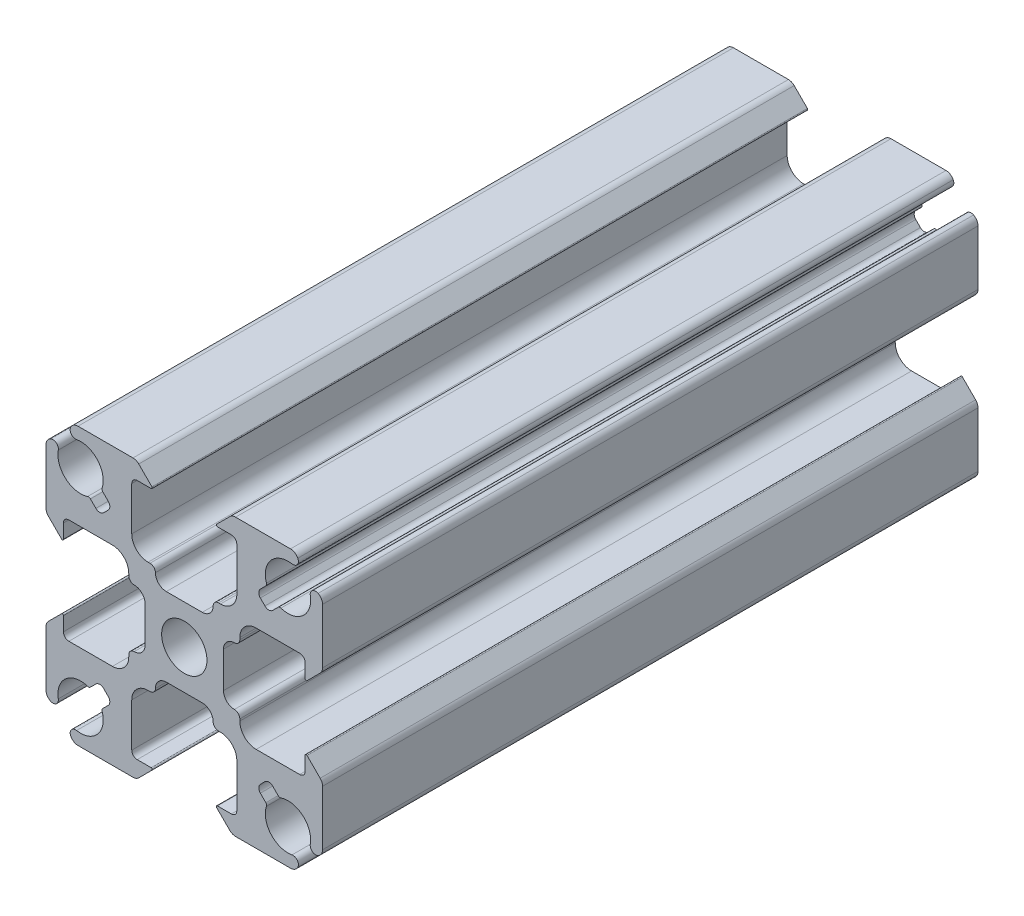
SolidWorks part; units mm, degrees
ref_plane "Front Plane" through (0, 0, 0) normal (0, 0, 1) x (1, 0, 0)
ref_plane "Top Plane" through (0, 0, 0) normal (0, 1, 0) x (1, 0, 0)
ref_plane "Right Plane" through (0, 0, 0) normal (1, 0, 0) x (0, 0, -1)
ref_plane "Plane1" through (0, 0, 0) normal (0, 0, -1) x (-1, 0, 0)
sketch "Sketch1" plane through (0, 0, 0) normal (0, 0, -1) x (-1, 0, 0)
  line L0 (-7.4885, 8.6199) -> (-6.9856, 8.117)
  line L1 (-6.9856, 7.4099) -> (-7.4099, 6.9856)
  line L2 (-8.117, 6.9856) -> (-8.6199, 7.4885)
  line L3 (-12.7, 9.7594) -> (-12.7, 4.7107)
  line L4 (-12.4803, 4.1803) -> (-11.2707, 2.9707)
  line L5 (-11.1, 3.0414) -> (-11.1, 4.325)
  line L6 (-10.6, 4.825) -> (-6.6, 4.825)
  line L7 (-5.1, 3.325) -> (-5.1, 3.15)
  line L8 (-3.6, 1.65) -> (-3.6, -1.65)
  line L9 (-5.1, -3.15) -> (-5.1, -3.325)
  line L10 (-6.6, -4.825) -> (-10.6, -4.825)
  line L11 (-11.1, -4.325) -> (-11.1, -3.0414)
  line L12 (-11.2707, -2.9707) -> (-12.4803, -4.1803)
  line L13 (-12.7, -4.7107) -> (-12.7, -9.7594)
  line L14 (-8.6199, -7.4885) -> (-8.117, -6.9856)
  line L15 (-7.4099, -6.9856) -> (-6.9856, -7.4099)
  line L16 (-6.9856, -8.117) -> (-7.4885, -8.6199)
  line L17 (-9.7594, -12.7) -> (-4.7107, -12.7)
  line L18 (-4.1803, -12.4803) -> (-2.9707, -11.2707)
  line L19 (-3.0414, -11.1) -> (-4.325, -11.1)
  line L20 (-4.825, -10.6) -> (-4.825, -6.6)
  line L21 (-3.325, -5.1) -> (-3.15, -5.1)
  line L22 (-1.65, -3.6) -> (1.65, -3.6)
  line L23 (3.15, -5.1) -> (3.325, -5.1)
  line L24 (4.825, -6.6) -> (4.825, -10.6)
  line L25 (4.325, -11.1) -> (3.0414, -11.1)
  line L26 (2.9707, -11.2707) -> (4.1803, -12.4803)
  line L27 (4.7107, -12.7) -> (9.7594, -12.7)
  line L28 (7.4885, -8.6199) -> (6.9856, -8.117)
  line L29 (6.9856, -7.4099) -> (7.4099, -6.9856)
  line L30 (8.117, -6.9856) -> (8.6199, -7.4885)
  line L31 (12.7, -9.7594) -> (12.7, -4.7107)
  line L32 (12.4803, -4.1803) -> (11.2707, -2.9707)
  line L33 (11.1, -3.0414) -> (11.1, -4.325)
  line L34 (10.6, -4.825) -> (6.6, -4.825)
  line L35 (5.1, -3.325) -> (5.1, -3.15)
  line L36 (3.6, -1.65) -> (3.6, 1.65)
  line L37 (5.1, 3.15) -> (5.1, 3.325)
  line L38 (6.6, 4.825) -> (10.6, 4.825)
  line L39 (11.1, 4.325) -> (11.1, 3.0414)
  line L40 (11.2707, 2.9707) -> (12.4803, 4.1803)
  line L41 (12.7, 4.7107) -> (12.7, 9.7594)
  line L42 (8.6199, 7.4885) -> (8.117, 6.9856)
  line L43 (7.4099, 6.9856) -> (6.9856, 7.4099)
  line L44 (6.9856, 8.117) -> (7.4885, 8.6199)
  line L45 (9.7594, 12.7) -> (4.7107, 12.7)
  line L46 (4.1803, 12.4803) -> (2.9707, 11.2707)
  line L47 (3.0414, 11.1) -> (4.325, 11.1)
  line L48 (4.825, 10.6) -> (4.825, 6.6)
  line L49 (3.325, 5.1) -> (3.15, 5.1)
  line L50 (1.65, 3.6) -> (-1.65, 3.6)
  line L51 (-3.15, 5.1) -> (-3.325, 5.1)
  line L52 (-4.825, 6.6) -> (-4.825, 10.6)
  line L53 (-4.325, 11.1) -> (-3.0414, 11.1)
  line L54 (-2.9707, 11.2707) -> (-4.1803, 12.4803)
  line L55 (-4.7107, 12.7) -> (-9.7594, 12.7)
  circle A0 centre (0, 0) radius 2.08
  arc A1 (-9.7594, 12.7) -> (-10.4266, 12.2927) centre (-9.7594, 11.95) ccw
  arc A2 (-10.4266, 12.2927) -> (-9.8933, 11.5721) centre (-9.9818, 12.0642) ccw
  arc A3 (-9.8933, 11.5721) -> (-7.5492, 8.8748) centre (-9.525, 9.525) cw
  arc A4 (-7.5492, 8.8748) -> (-7.4885, 8.6199) centre (-7.3118, 8.7967) ccw
  arc A5 (-6.9856, 8.117) -> (-6.9856, 7.4099) centre (-7.3392, 7.7635) cw
  arc A6 (-7.4099, 6.9856) -> (-8.117, 6.9856) centre (-7.7635, 7.3392) cw
  arc A7 (-8.6199, 7.4885) -> (-8.8748, 7.5492) centre (-8.7967, 7.3118) ccw
  arc A8 (-8.8748, 7.5492) -> (-11.5721, 9.8933) centre (-9.525, 9.525) cw
  arc A9 (-11.5721, 9.8933) -> (-12.2927, 10.4266) centre (-12.0642, 9.9818) ccw
  arc A10 (-12.2927, 10.4266) -> (-12.7, 9.7594) centre (-11.95, 9.7594) ccw
  arc A11 (-12.7, 4.7107) -> (-12.4803, 4.1803) centre (-11.95, 4.7107) ccw
  arc A12 (-11.2707, 2.9707) -> (-11.1, 3.0414) centre (-11.2, 3.0414) ccw
  arc A13 (-11.1, 4.325) -> (-10.6, 4.825) centre (-10.6, 4.325) cw
  arc A14 (-6.6, 4.825) -> (-5.1, 3.325) centre (-6.6, 3.325) cw
  arc A15 (-5.1, 3.15) -> (-4.6, 2.65) centre (-4.6, 3.15) ccw
  arc A16 (-4.6, 2.65) -> (-3.6, 1.65) centre (-4.6, 1.65) cw
  arc A17 (-3.6, -1.65) -> (-4.6, -2.65) centre (-4.6, -1.65) cw
  arc A18 (-4.6, -2.65) -> (-5.1, -3.15) centre (-4.6, -3.15) ccw
  arc A19 (-5.1, -3.325) -> (-6.6, -4.825) centre (-6.6, -3.325) cw
  arc A20 (-10.6, -4.825) -> (-11.1, -4.325) centre (-10.6, -4.325) cw
  arc A21 (-11.1, -3.0414) -> (-11.2707, -2.9707) centre (-11.2, -3.0414) ccw
  arc A22 (-12.4803, -4.1803) -> (-12.7, -4.7107) centre (-11.95, -4.7107) ccw
  arc A23 (-12.7, -9.7594) -> (-12.2927, -10.4266) centre (-11.95, -9.7594) ccw
  arc A24 (-12.2927, -10.4266) -> (-11.5721, -9.8933) centre (-12.0642, -9.9818) ccw
  arc A25 (-11.5721, -9.8933) -> (-8.8748, -7.5492) centre (-9.525, -9.525) cw
  arc A26 (-8.8748, -7.5492) -> (-8.6199, -7.4885) centre (-8.7967, -7.3118) ccw
  arc A27 (-8.117, -6.9856) -> (-7.4099, -6.9856) centre (-7.7635, -7.3392) cw
  arc A28 (-6.9856, -7.4099) -> (-6.9856, -8.117) centre (-7.3392, -7.7635) cw
  arc A29 (-7.4885, -8.6199) -> (-7.5492, -8.8748) centre (-7.3118, -8.7967) ccw
  arc A30 (-7.5492, -8.8748) -> (-9.8933, -11.5721) centre (-9.525, -9.525) cw
  arc A31 (-9.8933, -11.5721) -> (-10.4266, -12.2927) centre (-9.9818, -12.0642) ccw
  arc A32 (-10.4266, -12.2927) -> (-9.7594, -12.7) centre (-9.7594, -11.95) ccw
  arc A33 (-4.7107, -12.7) -> (-4.1803, -12.4803) centre (-4.7107, -11.95) ccw
  arc A34 (-2.9707, -11.2707) -> (-3.0414, -11.1) centre (-3.0414, -11.2) ccw
  arc A35 (-4.325, -11.1) -> (-4.825, -10.6) centre (-4.325, -10.6) cw
  arc A36 (-4.825, -6.6) -> (-3.325, -5.1) centre (-3.325, -6.6) cw
  arc A37 (-3.15, -5.1) -> (-2.65, -4.6) centre (-3.15, -4.6) ccw
  arc A38 (-2.65, -4.6) -> (-1.65, -3.6) centre (-1.65, -4.6) cw
  arc A39 (1.65, -3.6) -> (2.65, -4.6) centre (1.65, -4.6) cw
  arc A40 (2.65, -4.6) -> (3.15, -5.1) centre (3.15, -4.6) ccw
  arc A41 (3.325, -5.1) -> (4.825, -6.6) centre (3.325, -6.6) cw
  arc A42 (4.825, -10.6) -> (4.325, -11.1) centre (4.325, -10.6) cw
  arc A43 (3.0414, -11.1) -> (2.9707, -11.2707) centre (3.0414, -11.2) ccw
  arc A44 (4.1803, -12.4803) -> (4.7107, -12.7) centre (4.7107, -11.95) ccw
  arc A45 (9.7594, -12.7) -> (10.4266, -12.2927) centre (9.7594, -11.95) ccw
  arc A46 (10.4266, -12.2927) -> (9.8933, -11.5721) centre (9.9818, -12.0642) ccw
  arc A47 (9.8933, -11.5721) -> (7.5492, -8.8748) centre (9.525, -9.525) cw
  arc A48 (7.5492, -8.8748) -> (7.4885, -8.6199) centre (7.3118, -8.7967) ccw
  arc A49 (6.9856, -8.117) -> (6.9856, -7.4099) centre (7.3392, -7.7635) cw
  arc A50 (7.4099, -6.9856) -> (8.117, -6.9856) centre (7.7635, -7.3392) cw
  arc A51 (8.6199, -7.4885) -> (8.8748, -7.5492) centre (8.7967, -7.3118) ccw
  arc A52 (8.8748, -7.5492) -> (11.5721, -9.8933) centre (9.525, -9.525) cw
  arc A53 (11.5721, -9.8933) -> (12.2927, -10.4266) centre (12.0642, -9.9818) ccw
  arc A54 (12.2927, -10.4266) -> (12.7, -9.7594) centre (11.95, -9.7594) ccw
  arc A55 (12.7, -4.7107) -> (12.4803, -4.1803) centre (11.95, -4.7107) ccw
  arc A56 (11.2707, -2.9707) -> (11.1, -3.0414) centre (11.2, -3.0414) ccw
  arc A57 (11.1, -4.325) -> (10.6, -4.825) centre (10.6, -4.325) cw
  arc A58 (6.6, -4.825) -> (5.1, -3.325) centre (6.6, -3.325) cw
  arc A59 (5.1, -3.15) -> (4.6, -2.65) centre (4.6, -3.15) ccw
  arc A60 (4.6, -2.65) -> (3.6, -1.65) centre (4.6, -1.65) cw
  arc A61 (3.6, 1.65) -> (4.6, 2.65) centre (4.6, 1.65) cw
  arc A62 (4.6, 2.65) -> (5.1, 3.15) centre (4.6, 3.15) ccw
  arc A63 (5.1, 3.325) -> (6.6, 4.825) centre (6.6, 3.325) cw
  arc A64 (10.6, 4.825) -> (11.1, 4.325) centre (10.6, 4.325) cw
  arc A65 (11.1, 3.0414) -> (11.2707, 2.9707) centre (11.2, 3.0414) ccw
  arc A66 (12.4803, 4.1803) -> (12.7, 4.7107) centre (11.95, 4.7107) ccw
  arc A67 (12.7, 9.7594) -> (12.2927, 10.4266) centre (11.95, 9.7594) ccw
  arc A68 (12.2927, 10.4266) -> (11.5721, 9.8933) centre (12.0642, 9.9818) ccw
  arc A69 (11.5721, 9.8933) -> (8.8748, 7.5492) centre (9.525, 9.525) cw
  arc A70 (8.8748, 7.5492) -> (8.6199, 7.4885) centre (8.7967, 7.3118) ccw
  arc A71 (8.117, 6.9856) -> (7.4099, 6.9856) centre (7.7635, 7.3392) cw
  arc A72 (6.9856, 7.4099) -> (6.9856, 8.117) centre (7.3392, 7.7635) cw
  arc A73 (7.4885, 8.6199) -> (7.5492, 8.8748) centre (7.3118, 8.7967) ccw
  arc A74 (7.5492, 8.8748) -> (9.8933, 11.5721) centre (9.525, 9.525) cw
  arc A75 (9.8933, 11.5721) -> (10.4266, 12.2927) centre (9.9818, 12.0642) ccw
  arc A76 (10.4266, 12.2927) -> (9.7594, 12.7) centre (9.7594, 11.95) ccw
  arc A77 (4.7107, 12.7) -> (4.1803, 12.4803) centre (4.7107, 11.95) ccw
  arc A78 (2.9707, 11.2707) -> (3.0414, 11.1) centre (3.0414, 11.2) ccw
  arc A79 (4.325, 11.1) -> (4.825, 10.6) centre (4.325, 10.6) cw
  arc A80 (4.825, 6.6) -> (3.325, 5.1) centre (3.325, 6.6) cw
  arc A81 (3.15, 5.1) -> (2.65, 4.6) centre (3.15, 4.6) ccw
  arc A82 (2.65, 4.6) -> (1.65, 3.6) centre (1.65, 4.6) cw
  arc A83 (-1.65, 3.6) -> (-2.65, 4.6) centre (-1.65, 4.6) cw
  arc A84 (-2.65, 4.6) -> (-3.15, 5.1) centre (-3.15, 4.6) ccw
  arc A85 (-3.325, 5.1) -> (-4.825, 6.6) centre (-3.325, 6.6) cw
  arc A86 (-4.825, 10.6) -> (-4.325, 11.1) centre (-4.325, 10.6) cw
  arc A87 (-3.0414, 11.1) -> (-2.9707, 11.2707) centre (-3.0414, 11.2) ccw
  arc A88 (-4.1803, 12.4803) -> (-4.7107, 12.7) centre (-4.7107, 11.95) ccw
extrude "Boss-Extrude1" add sketch "Sketch1" against normal mid plane 60.197
